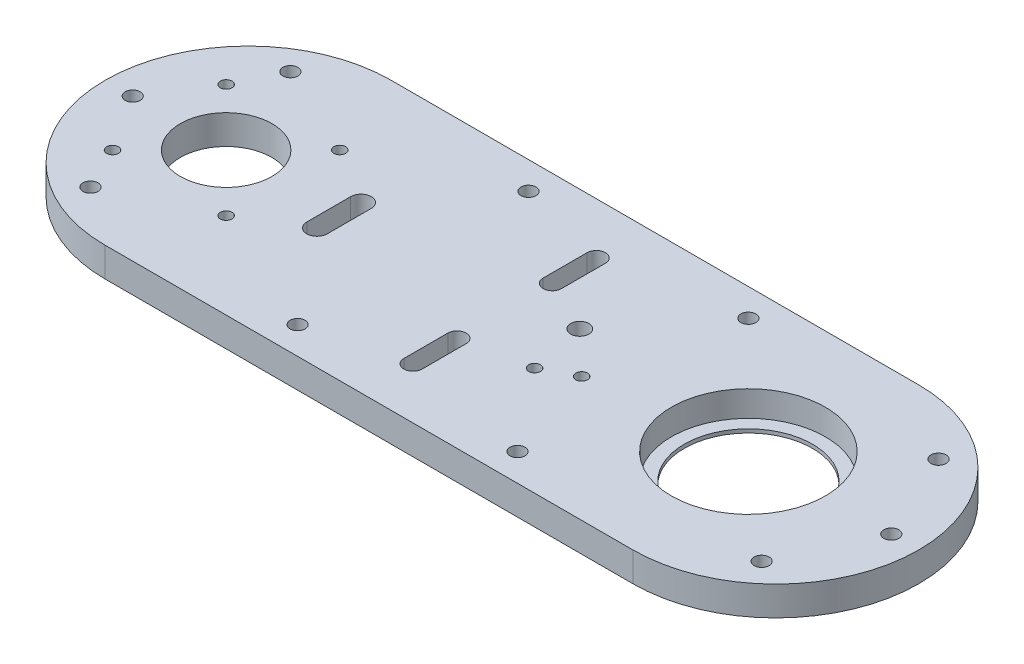
SolidWorks part; units mm, degrees
ref_plane "Front Plane" through (0, 0, 0) normal (0, 0, 1) x (1, 0, 0)
ref_plane "Top Plane" through (0, 0, 0) normal (0, 1, 0) x (1, 0, 0)
ref_plane "Right Plane" through (0, 0, 0) normal (1, 0, 0) x (0, 0, -1)
sketch "Sketch1" plane through (0, 0, 0) normal (0, 1, 0) x (1, 0, 0)
  line L0 (-144, 39) -> (0, 39)
  line L1 (0, -39) -> (-144, -39)
  arc A0 (0, -39) -> (0, 39) centre (0, 0) ccw
  arc A1 (-144, 39) -> (-144, -39) centre (-144, 0) ccw
  dimension "D1" = 78
  dimension "D2" = 78
  dimension "D3" = 144
extrude "Boss-Extrude1" add sketch "Sketch1" along normal blind 8
sketch "Sketch2" plane through (0, 8, 0) normal (0, 1, 0) x (1, 0, 0)
  line L0 (-150.9937, 6.2718) -> (-11.9835, 28.297) construction
  line L1 (-150.9937, -6.2718) -> (-11.9835, -28.297) construction
  line L2 (-150, 0) -> (-7.5, 0) construction
  line L3 (-7.5, 0) -> (0, 0) construction
  circle A0 centre (-7.5, 0) radius 17.5
  circle A1 centre (-150, 0) radius 12.5
  arc A2 (-150.9937, 6.2718) -> (-150.9937, -6.2718) centre (-150, 0) ccw construction
  arc A3 (-11.9835, -28.297) -> (-11.9835, 28.297) centre (-7.5, 0) ccw construction
  dimension "D1" = 35
  dimension "D2" = 25
  dimension "D3" = 142.5
  dimension "D4" = 12.7
  dimension "D5" = 57.3
  dimension "D6" = 7.5
extrude "Cut-Extrude1" cut sketch "Sketch2" against normal through all
sketch "Sketch3" plane through (0, 8, 0) normal (0, 1, 0) x (1, 0, 0)
  line L1 (-165.5, -15.5) -> (-134.5, -15.5) construction
  line L2 (-165.5, -15.5) -> (-165.5, 15.5) construction
  line L3 (-165.5, 15.5) -> (-134.5, 15.5) construction
  line L4 (-134.5, -15.5) -> (-134.5, 15.5) construction
  line L5 (-165.5, -15.5) -> (-134.5, 15.5) construction
  line L6 (-165.5, 15.5) -> (-134.5, -15.5) construction
  circle A0 centre (-165.5, 15.5) radius 1.6
  circle A1 centre (-134.5, 15.5) radius 1.6
  circle A2 centre (-134.5, -15.5) radius 1.6
  circle A3 centre (-165.5, -15.5) radius 1.6
  point P0 (-150, 0)
  dimension "D3" = 3.2
  dimension "D4" = 3.2
  dimension "D5" = 3.2
  dimension "D6" = 3.2
  dimension "D1" = 31
  dimension "D2" = 31
extrude "Cut-Extrude2" cut sketch "Sketch3" against normal through all
sketch "Sketch4" plane through (0, 8, 0) normal (0, 1, 0) x (1, 0, 0)
  line L0 (-144, 0) -> (-175.5, 0) construction
  line L1 (-144, 0) -> (-159.75, 27.2798) construction
  line L2 (-144, 0) -> (-159.75, -27.2798) construction
  line L3 (0, 0) -> (20.2478, 24.1304) construction
  line L4 (0, 0) -> (31.5, 0) construction
  line L5 (0, 0) -> (20.2478, -24.1304) construction
  line L6 (-99, 31.5) -> (-39, 31.5) construction
  line L7 (-144, 39) -> (-144, 0) construction
  circle A0 centre (-159.75, 27.2798) radius 2.05
  circle A1 centre (-175.5, 0) radius 2.05
  circle A2 centre (-159.75, -27.2798) radius 2.05
  circle A3 centre (20.2478, 24.1304) radius 2.05
  circle A4 centre (31.5, 0) radius 2.05
  circle A5 centre (20.2478, -24.1304) radius 2.05
  circle A6 centre (-99, 31.5) radius 2.05
  circle A7 centre (-39, 31.5) radius 2.05
  circle A8 centre (-39, -31.5) radius 2.05
  circle A9 centre (-99, -31.5) radius 2.05
  dimension "D6" = 4.1
  dimension "D7" = 4.1
  dimension "D8" = 4.1
  dimension "D14" = 4.1
  dimension "D15" = 4.1
  dimension "D16" = 4.1
  dimension "D19" = 4.1
  dimension "D1" = 60
  dimension "D2" = 31.5
  dimension "D3" = 31.5
  dimension "D4" = 31.5
  dimension "D5" = 60
  dimension "D9" = 50
  dimension "D10" = 50
  dimension "D11" = 31.5
  dimension "D12" = 31.5
  dimension "D13" = 31.5
  dimension "D17" = 31.5
  dimension "D18" = 45
  dimension "D21" = 60
  dimension "D20" = 2
extrude "Cut-Extrude3" cut sketch "Sketch4" against normal through all
sketch "Sketch5" plane through (0, 8, 0) normal (0, 1, 0) x (1, 0, 0)
  line L0 (-74, -25) -> (-74, -13) construction
  line L1 (-76.5, -25) -> (-76.5, -13)
  line L2 (-71.5, -25) -> (-71.5, -13)
  line L3 (-74, 25) -> (-74, 13) construction
  line L4 (-71.5, 25) -> (-71.5, 13)
  line L5 (-76.5, 25) -> (-76.5, 13)
  line L6 (0, 39) -> (-144, 39) construction
  line L7 (-144, -39) -> (0, -39) construction
  arc A0 (-76.5, -25) -> (-71.5, -25) centre (-74, -25) ccw
  arc A1 (-71.5, -13) -> (-76.5, -13) centre (-74, -13) ccw
  arc A2 (-71.5, 25) -> (-76.5, 25) centre (-74, 25) ccw
  arc A3 (-76.5, 13) -> (-71.5, 13) centre (-74, 13) ccw
  point P2 (-74, -19)
  point P7 (-74, 19)
  dimension "D1" = 2.5
  dimension "D5" = 2.5
  dimension "D2" = 12
  dimension "D3" = 14
  dimension "D4" = 12
  dimension "D6" = 14
  dimension "D7" = 74
extrude "Cut-Extrude4" cut sketch "Sketch5" against normal through all
sketch "Sketch6" plane through (0, 8, 0) normal (0, 1, 0) x (1, 0, 0)
  line L0 (-144, -39) -> (0, -39) construction
  line L1 (-48, -5) -> (-56.388, -9.46) construction
  line L2 (0, 39) -> (-144, 39) construction
  circle A0 centre (-48, -5) radius 1.6
  circle A1 centre (-56.388, -9.46) radius 1.6
  circle A2 centre (-59.5, 6) radius 2.5
  circle A3 centre (-7.5, 0) radius 17.5 construction
  dimension "D4" = 3.2
  dimension "D5" = 3.2
  dimension "D7" = 5
  dimension "D9" = 52
  dimension "D1" = 40.5
  dimension "D2" = 34
  dimension "D3" = 9.5
  dimension "D6" = 28
  dimension "D8" = 33
extrude "Cut-Extrude5" cut sketch "Sketch6" against normal through all
sketch "Sketch7" plane through (0, 8, 0) normal (0, 1, 0) x (1, 0, 0)
  circle A0 centre (-7.5, 0) radius 21
  dimension "D1" = 42
extrude "Cut-Extrude6" cut sketch "Sketch7" against normal blind 7
hole_wizard "CSK for M4 Countersunk Flat Head Screw1" positions "3DSketch1" profile "Sketch8" countersink size "M4" standard "ISO"
sketch3d "3DSketch1"
  line L0 (-159.75, 0, 27.2798) -> (-159.75, 8, 27.2798) construction
  line L1 (-175.5, 0, 0) -> (-175.5, 8, 0) construction
  line L2 (-159.75, 0, -27.2798) -> (-159.75, 8, -27.2798) construction
  line L3 (-99, 0, 31.5) -> (-99, 8, 31.5) construction
  line L4 (-99, 0, -31.5) -> (-99, 8, -31.5) construction
  line L5 (-39, 0, 31.5) -> (-39, 8, 31.5) construction
  line L6 (-39, 0, -31.5) -> (-39, 8, -31.5) construction
  line L7 (20.2478, 0, 24.1304) -> (20.2478, 8, 24.1304) construction
  line L8 (31.5, 0, 0) -> (31.5, 8, 0) construction
  line L9 (20.2478, 0, -24.1304) -> (20.2478, 8, -24.1304) construction
  point P0 (-159.75, 0, 27.2798)
  point P4 (-175.5, 0, 0)
  point P8 (-159.75, 0, -27.2798)
  point P12 (-99, 0, 31.5)
  point P16 (-99, 0, -31.5)
  point P20 (-39, 0, 31.5)
  point P24 (-39, 0, -31.5)
  point P28 (20.2478, 0, 24.1304)
  point P32 (31.5, 0, 0)
  point P36 (20.2478, 0, -24.1304)
sketch "Sketch8" plane through (-159.75, 0, 27.2798) normal (1, 0, 0) x (0, 0, -1)
  line L0 (0, 0) -> (0, 8)
  line L1 (0, 8) -> (2.05, 8)
  line L2 (2.05, 8) -> (2.05, 2.5)
  line L3 (2.05, 2.5) -> (4.55, 0)
  line L5 (4.55, 0) -> (0, 0)
  line L6 (-2.05, 2.5) -> (-4.55, 0) construction
  line L11 (0, -6.35) -> (0, 107.95) construction
  dimension "Thru Hole Dia." = 4.1
  dimension "Thru Hole Depth" = 8
  dimension "Near C'Sink Dia." = 9.1
  dimension "Near C'Sink Angle" = 90
sketch "Sketch9" plane through (0, 8, 0) normal (0, 1, 0) x (1, 0, 0)
  line L0 (-119.2, -6) -> (-119.2, 6) construction
  line L1 (-122, -6) -> (-122, 6)
  line L2 (-116.4, -6) -> (-116.4, 6)
  arc A0 (-122, -6) -> (-116.4, -6) centre (-119.2, -6) ccw
  arc A1 (-116.4, 6) -> (-122, 6) centre (-119.2, 6) ccw
  circle A2 centre (-150, 0) radius 12.5 construction
  point P2 (-119.2, 0)
  dimension "D2" = 2.8
  dimension "D3" = 12
  dimension "D1" = 28
extrude "Cut-Extrude7" cut sketch "Sketch9" against normal through all
